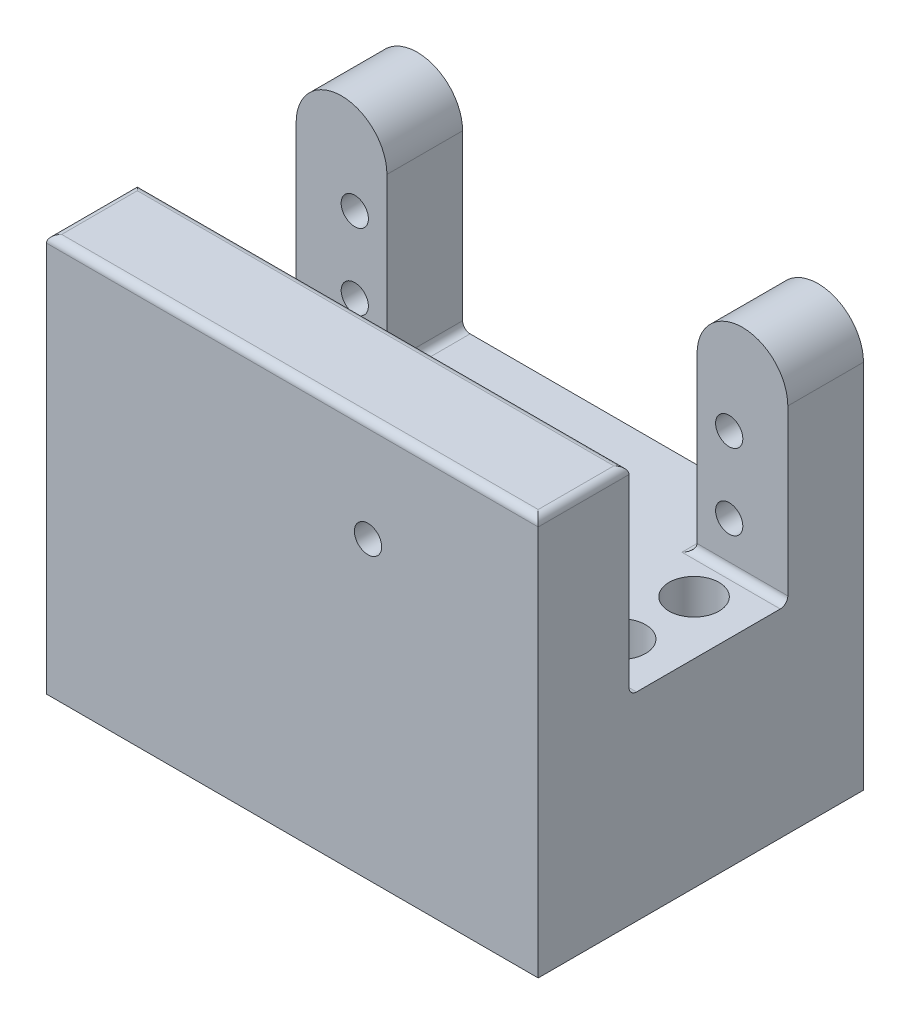
SolidWorks part; units mm, degrees
ref_plane "Front Plane" through (0, 0, 0) normal (0, 0, 1) x (1, 0, 0)
ref_plane "Top Plane" through (0, 0, 0) normal (0, 1, 0) x (1, 0, 0)
ref_plane "Right Plane" through (0, 0, 0) normal (1, 0, 0) x (0, 0, -1)
sketch "Sketch1" plane through (0, 0, 0) normal (0, 0, 1) x (1, 0, 0)
  line L0 (0, 25.9884) -> (0, -27.0349) construction
  line L1 (-6, 14.3023) -> (-6, -20.6977)
  line L2 (6, 14.3023) -> (6, -20.6977)
  line L3 (-6, -20.6977) -> (6, -20.6977)
  arc A0 (-6, 14.3023) -> (6, 14.3023) centre (0, 14.3023) cw
  dimension "D1" = 35
  dimension "D2" = 12
extrude "Boss-Extrude1" add sketch "Sketch1" along normal blind 10
sketch "Sketch2" plane through (0, 0, 10) normal (0, 0, 1) x (1, 0, 0)
  line L0 (6, -20.6977) -> (6, 14.3023) construction
  line L1 (-6, -20.6977) -> (6, -20.6977)
  line L2 (-6, -20.6977) -> (-6, -8.4477)
  line L3 (-6, -8.4477) -> (6, -8.4477)
  line L4 (6, -20.6977) -> (6, -8.4477)
  dimension "D1" = 12.25
extrude "Boss-Extrude2" add sketch "Sketch2" along normal blind 21 contours L3 L4 L1 L2
sketch "Sketch4" plane through (0, 0, 31) normal (0, 0, 1) x (1, 0, 0)
  line L1 (6, -20.6977) -> (-59, -20.6977)
  line L2 (6, -20.6977) -> (6, 17.9393)
  line L3 (6, 17.9393) -> (-59, 17.9393)
  line L4 (-59, -20.6977) -> (-59, 17.9393)
  dimension "D1" = 65
extrude "Boss-Extrude3" add sketch "Sketch4" along normal blind 12
ref_plane "Plane1" through (-26.5, 0, 0) normal (-1, 0, 0) x (0, 0, 1)
sketch "Sketch11" plane through (0, 0, 0) normal (0, 0, -1) x (-1, 0, 0)
  circle A0 centre (51.25, 8) radius 1.5
  circle A1 centre (51.25, -2) radius 1.5
  circle A3 centre (1.75, 7.5522) radius 1.5
  circle A4 centre (1.75, -2.4478) radius 1.5
  dimension "D1" = 49.5
  dimension "D4" = 3
  dimension "D5" = 3
  dimension "D6" = 3
  dimension "D7" = 3
  dimension "D2" = 10
  dimension "D3" = 49.5
  dimension "D8" = 10
mirror "Mirror2" about plane through (-26.5, 0, 0) normal (-1, 0, 0) of "Boss-Extrude2"
mirror "Mirror3" about plane through (-26.5, 0, 0) normal (-1, 0, 0) of "Boss-Extrude1"
hole_wizard "Ø3.6 (3.6) Diameter Hole1" positions "Sketch14" profile "Sketch15" hole size "Ø3.6" standard "ANSI Metric"
sketch "Sketch14" plane through (0, 0, 0) normal (0, 0, -1) x (-1, 0, 0)
  point P0 (1.75, 7.5522)
  point P3 (1.75, -2.4478)
  point P6 (51.25, 8)
  point P9 (51.25, -2)
sketch "Sketch15" plane through (-1.75, 7.5522, 0) normal (1, 0, 0) x (0, 1, 0)
  line L0 (0, 0) -> (0, 11.0815)
  line L1 (0, 11.0815) -> (1.8, 10)
  line L2 (1.8, 10) -> (1.8, 0)
  line L5 (1.8, 0) -> (0, 0)
  line L10 (0, 11.0815) -> (-1.8, 10) construction
  line L11 (0, -6.35) -> (0, 107.95) construction
  dimension "Hole Dia." = 3.6
  dimension "Hole Depth" = 10
  dimension "Drill Angle" = 118
hole_wizard "Ø3.6 (3.6) Diameter Hole2" positions "Sketch19" profile "Sketch20" hole size "Ø3.6" standard "ANSI Metric"
sketch "Sketch19" plane through (0, 0, 43) normal (0, 0, 1) x (1, 0, 0)
  point P0 (-16.5, 4.3132)
sketch "Sketch20" plane through (-16.5, 4.3132, 43) normal (1, 0, 0) x (0, -1, 0)
  line L0 (0, 0) -> (0, 13.0815)
  line L1 (0, 13.0815) -> (1.8, 12)
  line L2 (1.8, 12) -> (1.8, 0)
  line L5 (1.8, 0) -> (0, 0)
  line L10 (0, 13.0815) -> (-1.8, 12) construction
  line L11 (0, -6.35) -> (0, 107.95) construction
  dimension "Hole Dia." = 3.6
  dimension "Hole Depth" = 12
  dimension "Drill Angle" = 118
sketch "Sketch21" plane through (0, 0, 31) normal (0, 0, -1) x (-1, 0, 0)
  line L1 (6, -8.4477) -> (47, -8.4477)
  line L2 (6, -8.4477) -> (6, -20.6977)
  line L3 (6, -20.6977) -> (47, -20.6977)
  line L4 (47, -8.4477) -> (47, -20.6977)
extrude "Boss-Extrude4" add sketch "Sketch21" along normal up to surface (31 mm away) up to face at (-3.55, 7.5522, 0)
sketch "Sketch23" plane through (0, -20.6977, 0) normal (0, -1, 0) x (1, 0, 0)
  line L1 (-59, 43) -> (6, 43)
  line L2 (-59, 43) -> (-59, 0)
  line L3 (-59, 0) -> (6, 0)
  line L4 (6, 43) -> (6, 0)
extrude "Boss-Extrude6" add sketch "Sketch23" along normal blind 14
sketch "Sketch24" plane through (0, -34.6977, 0) normal (0, -1, 0) x (-1, 0, 0)
  line L0 (-37.3158, -15.3) -> (71.6842, -15.3) construction
  line L5 (59, -43) -> (59, 0) construction
  line L6 (-6, 0) -> (-6, -43) construction
  circle A0 centre (1.1, -25) radius 3
  circle A1 centre (1.1, -15.3) radius 3
  circle A2 centre (51.9, -25) radius 3
  circle A3 centre (51.9, -15.3) radius 3
  dimension "D3" = 6
  dimension "D4" = 6
  dimension "D5" = 6
  dimension "D6" = 6
  dimension "D1" = 7.1
  dimension "D8" = 7.1
hole_wizard "Ø6.6 (6.6) Diameter Hole1" positions "Sketch25" profile "Sketch26" hole size "Ø6.6" standard "ANSI Metric" end condition through all
sketch "Sketch25" plane through (0, -34.6977, 0) normal (0, -1, 0) x (-1, 0, 0)
  point P0 (1.1, -15.3)
  point P3 (1.1, -25)
  point P6 (51.9, -15.3)
  point P9 (51.9, -25)
sketch "Sketch26" plane through (-1.1, -34.6977, 15.3) normal (1, 0, 0) x (0, 0, -1)
  line L0 (0, 0) -> (0, 55)
  line L1 (0, 55) -> (3.3, 55)
  line L2 (3.3, 55) -> (3.3, 0)
  line L5 (3.3, 0) -> (0, 0)
  line L11 (0, -6.35) -> (0, 107.95) construction
  dimension "Thru Hole Dia." = 6.6
  dimension "Thru Hole Depth" = 55
fillet "Fillet1" radius 1 9 edges at (-26.5, -8.4477, 31) (0, -8.4477, 10) (-26.5, 17.9393, 31) (6, 17.9393, 37) (-59, 17.9393, 37) (-26.5, 17.9393, 43) (-53, -8.4477, 10) (-6, -8.4477, 5) (-47, -8.4477, 5)
